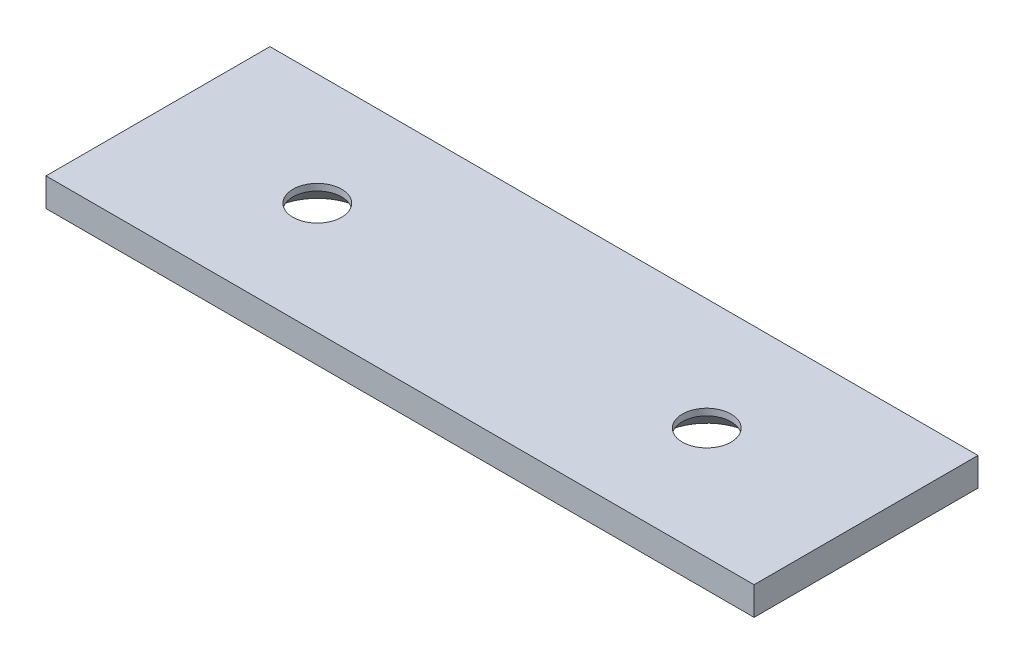
SolidWorks part; units mm, degrees
ref_plane "Front Plane" through (0, 0, 0) normal (0, 0, 1) x (1, 0, 0)
ref_plane "Top Plane" through (0, 0, 0) normal (0, 1, 0) x (1, 0, 0)
ref_plane "Right Plane" through (0, 0, 0) normal (1, 0, 0) x (0, 0, -1)
sketch "Sketch1" plane through (0, 0, 0) normal (0, 1, 0) x (1, 0, 0)
  line L1 (0, 0) -> (80, 0)
  line L2 (0, 0) -> (0, -25.3)
  line L3 (0, -25.3) -> (80, -25.3)
  line L4 (80, 0) -> (80, -25.3)
  dimension "D1" = 80
  dimension "D2" = 25.3
extrude "Boss-Extrude1" add sketch "Sketch1" along normal blind 3.2
hole_wizard "CSK for M5 Flat Head Machine Screw1" positions "Sketch2" profile "Sketch3" countersink size "M5" standard "ANSI Metric" end condition up to next
sketch "Sketch2" plane through (0, 0, 0) normal (0, -1, 0) x (-1, 0, 0)
  point P0 (-62, -12.65)
  point P3 (-18, -12.65)
sketch "Sketch3" plane through (62, 0, 12.65) normal (1, 0, 0) x (0, 0, -1)
  line L0 (0, 0) -> (0, 3.2)
  line L1 (0, 3.2) -> (2.75, 3.2)
  line L2 (2.75, 3.2) -> (2.75, 2.45)
  line L3 (2.75, 2.45) -> (5.2, 0)
  line L5 (5.2, 0) -> (0, 0)
  line L6 (-2.75, 2.45) -> (-5.2, 0) construction
  line L11 (0, -6.35) -> (0, 107.95) construction
  dimension "Thru Hole Dia." = 5.5
  dimension "Thru Hole Depth" = 3.2
  dimension "Near C'Sink Dia." = 10.4
  dimension "Near C'Sink Angle" = 90
